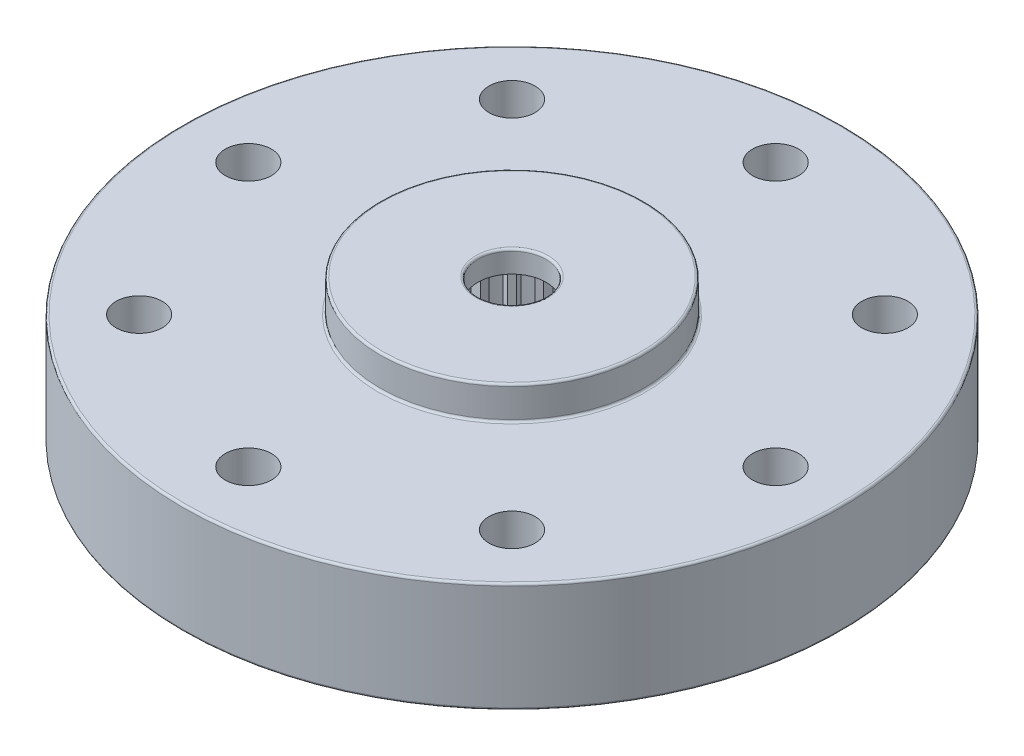
SolidWorks part; units mm, degrees
ref_plane "Plan de face" through (0, 0, 0) normal (0, 0, 1) x (1, 0, 0)
ref_plane "Plan de dessus" through (0, 0, 0) normal (0, 1, 0) x (1, 0, 0)
ref_plane "Plan de droite" through (0, 0, 0) normal (1, 0, 0) x (0, 0, -1)
sketch "Esquisse2" plane through (0, 0, 0) normal (0, 1, 0) x (1, 0, 0)
  circle A0 centre (0, 0) radius 15
  circle A1 centre (0, 0) radius 1.55
  dimension "D1" = 30
  dimension "D2" = 3.1
extrude "Boss.-Extru.1" add sketch "Esquisse2" along normal blind 6.5
sketch "Esquisse3" plane through (0, 6.5, 0) normal (0, 1, 0) x (1, 0, 0)
  circle A0 centre (0, 0) radius 6
  circle A1 centre (0, 0) radius 15
  circle A2 centre (0, 0) radius 15 construction
  dimension "D1" = 12
extrude "Enlèv. mat.-Extru.1" cut sketch "Esquisse3" against normal blind 1.5
fillet "Congé1" radius 0.1 5 edges at (0, 0, 15) (0, 5, 15) (0, 5, 6) (0, 6.5, 6) (0, 6.5, 1.55)
sketch "Esquisse4" plane through (0, 0, 0) normal (0, -1, 0) x (1, 0, 0)
  circle A0 centre (0, 12) radius 1.05
  point P2 (0, 0)
  point P5 (-29.7592, 15.5802)
  dimension "D1" = 2.1
  dimension "D2" = 12
extrude "Enlèv. mat.-Extru.2" cut sketch "Esquisse4" against normal blind 5
pattern_circular "Répétition circulaire1" count 8 over 360 about axis through (0, 0, 0) along (0, 1, 0) of "Enlèv. mat.-Extru.2"
sketch "Esquisse5" plane through (0, 0, 0) normal (0, -1, 0) x (1, 0, 0)
  circle A0 centre (0, 0) radius 4
  dimension "D1" = 8
extrude "Enlèv. mat.-Extru.3" cut sketch "Esquisse5" against normal blind 5.5
sketch "Esquisse6" plane through (0, 0, 0) normal (0, -1, 0) x (1, 0, 0)
  line L0 (0, 0) -> (0, 10.3519) construction
  line L1 (0, 0) -> (8.7625, 0) construction
  line L2 (1.1, 8.7062) -> (1.1, 6.4062)
  line L3 (6.4062, 1.1) -> (8.7062, 1.1)
  arc A0 (1.1, 6.4062) -> (6.4062, 1.1) centre (0, 0) cw
  arc A1 (1.1, 8.7062) -> (8.7062, 1.1) centre (0, 0) cw
  dimension "D3" = 6.5
  dimension "D1" = 2.2
  dimension "D2" = 1.1
  dimension "D4" = 2.3
extrude "Enlèv. mat.-Extru.4" cut sketch "Esquisse6" against normal blind 2.5
fillet "Congé2" radius 0.25 4 edges at (8.7062, 1.25, 1.1) (6.4062, 1.25, 1.1) (1.1, 1.25, 6.4062) (1.1, 1.25, 8.7062)
pattern_circular "Répétition circulaire2" count 4 over 360 about axis through (0, 0, 0) along (0, 1, 0) of "Enlèv. mat.-Extru.4", "Congé2"
sketch "Esquisse7" plane through (0, 0, 0) normal (0, -1, 0) x (1, 0, 0)
  line L0 (0, 0) -> (0, 5.3406) construction
  line L1 (0, 5.3406) -> (-2.3501, 4) construction
  line L2 (-2.3501, 4) -> (2.3948, 4) construction
  line L5 (0.3, 4) -> (-0.3, 4)
  line L6 (-0.3, 4) -> (-0.1392, 3.4)
  line L7 (-0.1392, 3.4) -> (0.1392, 3.4)
  line L8 (0.1392, 3.4) -> (0.3, 4)
  circle A0 centre (0, 0) radius 4 construction
  dimension "D1" = 0.6
  dimension "D2" = 15
  dimension "D3" = 0.6
extrude "Boss.-Extru.2" add sketch "Esquisse7" against normal up to surface (5.5 mm away) up to face at (0, 5.5, -1.55)
pattern_circular "Répétition circulaire3" count 24 over 360 about axis through (0, 0, 0) along (0, 1, 0) of "Boss.-Extru.2"
